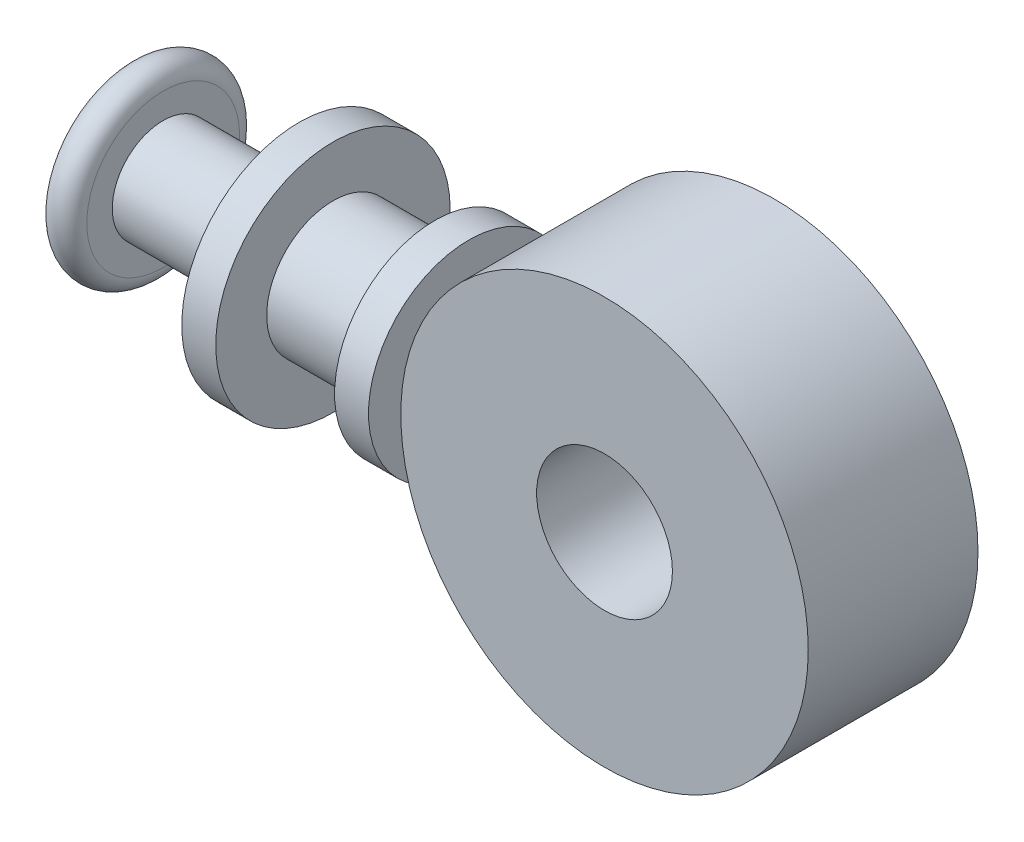
SolidWorks part; units mm, degrees
material "AISI 1035 Steel (SS)"
ref_plane "Front Plane" through (0, 0, 0) normal (0, 0, 1) x (1, 0, 0)
ref_plane "Top Plane" through (0, 0, 0) normal (0, 1, 0) x (1, 0, 0)
ref_plane "Right Plane" through (0, 0, 0) normal (1, 0, 0) x (0, 0, -1)
sketch "Sketch1" plane through (0, 0, 0) normal (0, 0, 1) x (1, 0, 0)
  circle A0 centre (0, 0) radius 9.4107
  circle A1 centre (0, 0) radius 3.1369
extrude "Boss-Extrude1" add sketch "Sketch1" along normal blind 3.9205 and the other way blind 3.9205
sketch "Sketch2" plane through (0, 0, 0) normal (0, 1, 0) x (1, 0, 0)
  line L0 (-5.9592, 0) -> (-25.875, 0)
  line L1 (-25.875, 0) -> (-25.875, 3.5293)
  line L3 (-24.3078, 3.5293) -> (-24.3078, 2.352)
  line L4 (-24.3078, 2.352) -> (-18.034, 2.352)
  line L5 (-18.034, 2.352) -> (-18.034, 5.4153)
  line L6 (-18.034, 5.4153) -> (-16.4643, 5.4153)
  line L7 (-16.4643, 5.4153) -> (-16.4643, 3.062)
  line L8 (-16.4643, 3.062) -> (-11.7602, 3.062)
  line L9 (-11.7602, 3.062) -> (-11.7602, 4.6304)
  line L10 (-11.7602, 4.6304) -> (-10.193, 4.6304)
  line L11 (-10.193, 4.6304) -> (-10.193, 2.352)
  line L12 (-10.193, 2.352) -> (-5.9592, 2.352)
  line L13 (-5.9592, 2.352) -> (-5.9592, 0)
  arc A0 (-24.3078, 3.5293) -> (-25.875, 3.5293) centre (-25.0914, 3.5293) ccw
  dimension "D2" = 6.2738
  dimension "D3" = 1.5697
  dimension "D4" = 4.7041
  dimension "D5" = 1.5672
  dimension "D7" = 2.352
  dimension "D8" = 5.4153
  dimension "D9" = 3.062
  dimension "D10" = 4.6304
  dimension "D11" = 2.352
revolve "Revolve1" add sketch "Sketch2" angle 360 about L0
